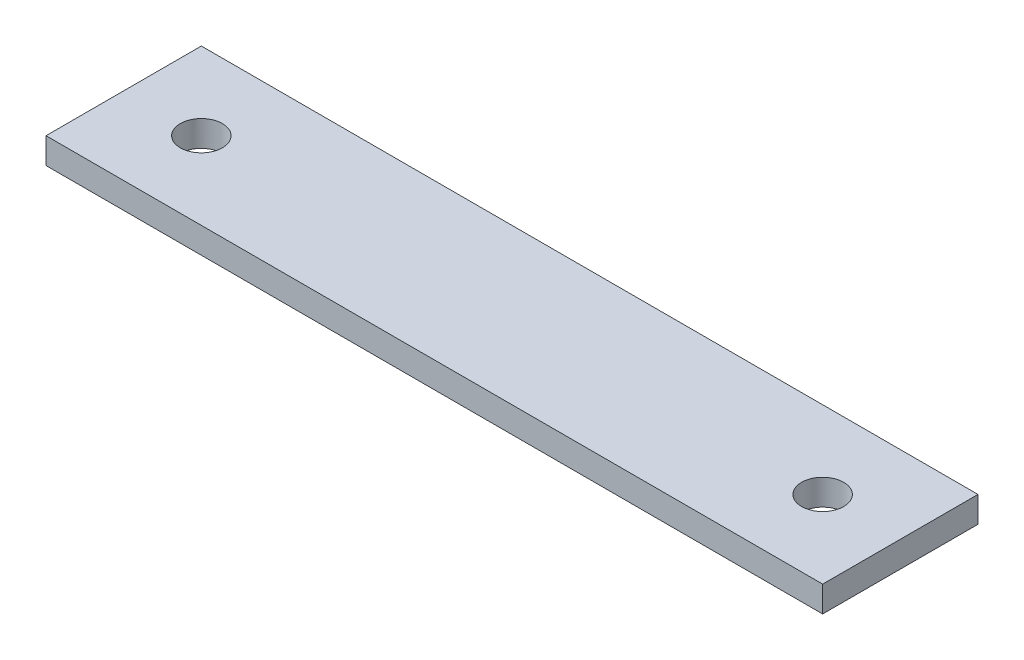
SolidWorks part; units mm, degrees
ref_plane "Front Plane" through (0, 0, 0) normal (0, 0, 1) x (1, 0, 0)
ref_plane "Top Plane" through (0, 0, 0) normal (0, 1, 0) x (1, 0, 0)
ref_plane "Right Plane" through (0, 0, 0) normal (1, 0, 0) x (0, 0, -1)
sketch "Sketch1" plane through (0, 0, 0) normal (0, 1, 0) x (1, 0, 0)
  line L1 (0, 0) -> (381, 0)
  line L2 (0, 0) -> (0, 76.2)
  line L3 (0, 76.2) -> (381, 76.2)
  line L4 (381, 0) -> (381, 76.2)
  dimension "D1" = 76.2
  dimension "D2" = 381
extrude "Boss-Extrude1" add sketch "Sketch1" along normal blind 12.7
sketch "Sketch2" plane through (0, 12.7, 0) normal (0, 1, 0) x (1, 0, 0)
  line L0 (0, 76.2) -> (0, 0) construction
  line L1 (0, 0) -> (381, 0) construction
  line L2 (190.5, 76.2) -> (190.5, 0) construction
  line L3 (381, 76.2) -> (0, 76.2) construction
  circle A0 centre (38.1, 38.1) radius 10.3187
  circle A1 centre (342.9, 38.1) radius 10.3188
  dimension "D3" = 20.6375
  dimension "D1" = 38.1
  dimension "D2" = 38.1
extrude "Cut-Extrude1" cut sketch "Sketch2" against normal up to next
